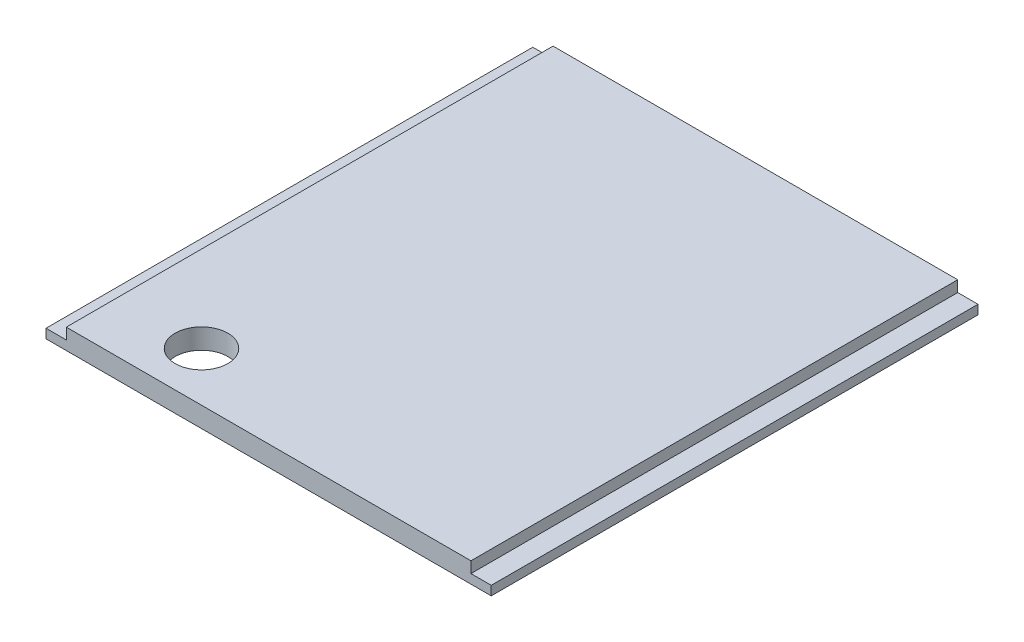
SolidWorks part; units mm, degrees
ref_plane "Front Plane" through (0, 0, 0) normal (0, 0, 1) x (1, 0, 0)
ref_plane "Top Plane" through (0, 0, 0) normal (0, 1, 0) x (1, 0, 0)
ref_plane "Right Plane" through (0, 0, 0) normal (1, 0, 0) x (0, 0, -1)
sketch "Sketch1" plane through (0, 0, 0) normal (0, 1, 0) x (1, 0, 0)
  line L1 (0, 0) -> (139.4003, 0)
  line L2 (0, 0) -> (0, 152.4)
  line L3 (0, 152.4) -> (139.4003, 152.4)
  line L4 (139.4003, 0) -> (139.4003, 152.4)
  dimension "D1" = 152.4
  dimension "D2" = 139.4003
extrude "Boss-Extrude1" add sketch "Sketch1" along normal blind 6.35
sketch "Sketch2" plane through (0, 6.35, 0) normal (0, 1, 0) x (1, 0, 0)
  line L0 (0, 0) -> (139.4003, 0) construction
  line L1 (0, 152.4) -> (6.35, 152.4)
  line L2 (0, 152.4) -> (0, 0)
  line L3 (0, 0) -> (6.35, 0)
  line L4 (6.35, 152.4) -> (6.35, 0)
  line L6 (139.4003, 152.4) -> (133.0503, 152.4)
  line L7 (139.4003, 152.4) -> (139.4003, 0)
  line L8 (139.4003, 0) -> (133.0503, 0)
  line L9 (133.0503, 152.4) -> (133.0503, 0)
  dimension "D1" = 6.35
  dimension "D2" = 6.35
extrude "Cut-Extrude1" cut sketch "Sketch2" against normal blind 3.4747
sketch "Sketch3" plane through (0, 6.35, 0) normal (0, 1, 0) x (1, 0, 0)
  line L0 (6.35, 0) -> (133.0503, 0) construction
  line L1 (6.35, 0) -> (6.35, 152.4) construction
  line L2 (0, 152.4) -> (0, 0) construction
  circle A0 centre (33.274, 15.4084) radius 8.255
  point P8 (0, 0)
  dimension "D1" = 16.51
  dimension "D2" = 15.4084
  dimension "D3" = 26.924
  dimension "D4" = 33.274
extrude "Cut-Extrude2" cut sketch "Sketch3" against normal through all
